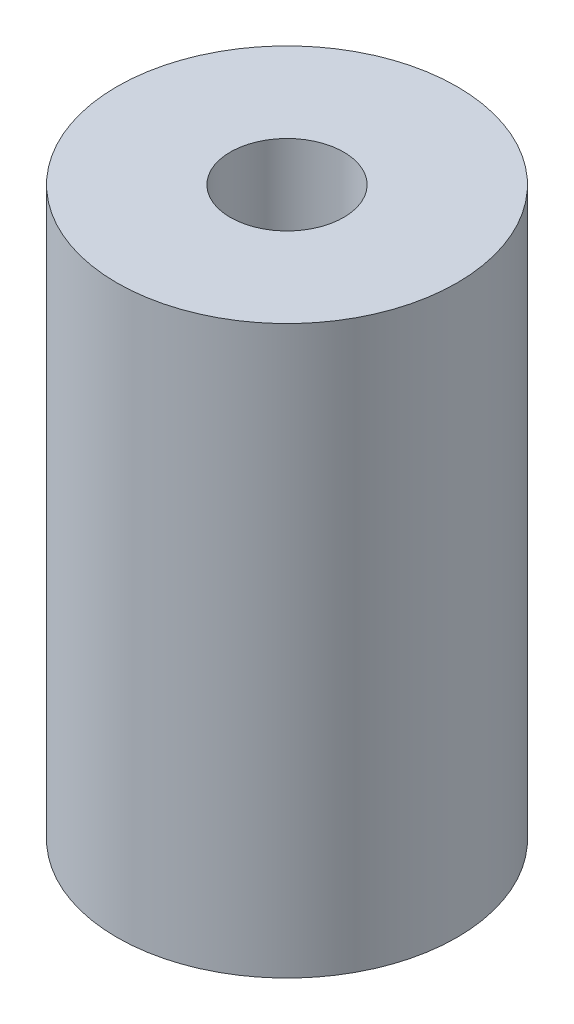
SolidWorks part; units mm, degrees
ref_plane "Front" through (0, 0, 0) normal (0, 0, 1) x (1, 0, 0)
ref_plane "Top" through (0, 0, 0) normal (0, 1, 0) x (1, 0, 0)
ref_plane "Right" through (0, 0, 0) normal (1, 0, 0) x (0, 0, -1)
sketch "Sketch1" plane through (0, 0, 0) normal (0, 1, 0) x (1, 0, 0)
  circle A0 centre (0, 0) radius 3.175
  circle A1 centre (0, 0) radius 9.525
  dimension "D1" = 6.35
  dimension "D2" = 19.05
extrude "Boss-Extrude1" add sketch "Sketch1" along normal blind 31.75
